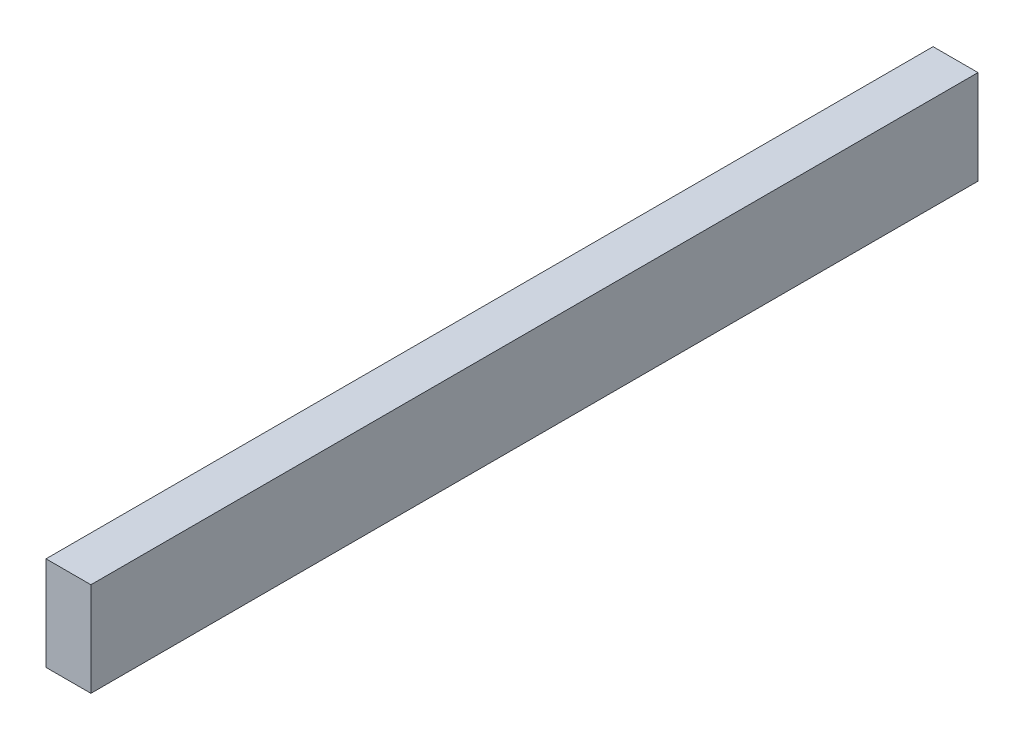
SolidWorks part; units mm, degrees
ref_plane "前视基准面" through (0, 0, 0) normal (0, 0, 1) x (1, 0, 0)
ref_plane "上视基准面" through (0, 0, 0) normal (0, 1, 0) x (1, 0, 0)
ref_plane "右视基准面" through (0, 0, 0) normal (1, 0, 0) x (0, 0, -1)
ref_plane "基准面1" through (0, 0, 400) normal (0, 0, 1) x (1, 0, 0)
sketch "草图1" plane through (0, 0, 400) normal (0, 0, 1) x (1, 0, 0)
  line L0 (0, 0) -> (0, -825.3602)
  line L2 (-7.5932, -533.3383) -> (7.5932, -533.3383)
  line L3 (-7.5932, -533.3383) -> (-7.5932, -565.1512)
  line L4 (-7.5932, -565.1512) -> (7.5932, -565.1512)
  line L5 (7.5932, -533.3383) -> (7.5932, -565.1512)
  line L6 (-7.5932, -533.3383) -> (7.5932, -565.1512) construction
  line L7 (-7.5932, -565.1512) -> (7.5932, -533.3383) construction
  point P3 (0, -549.2448)
extrude "凸台-拉伸1" add sketch "草图1" along normal blind 300 contours L3 L4 L0 L2 | L5 L2 L0 L4
